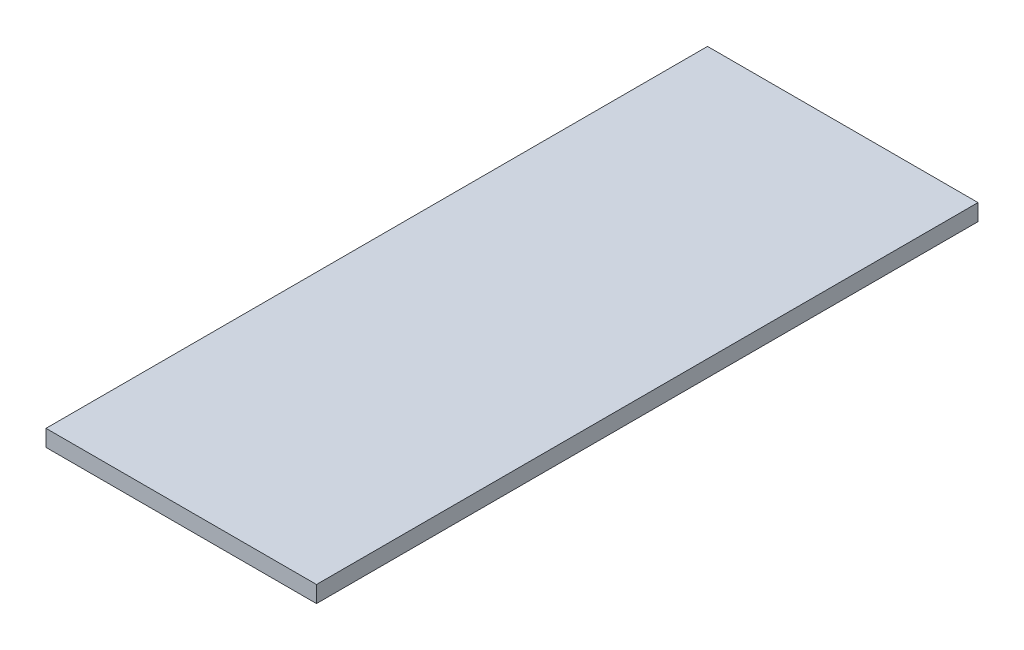
SolidWorks part; units mm, degrees
ref_plane "Спереди" through (0, 0, 0) normal (0, 0, 1) x (1, 0, 0)
ref_plane "Сверху" through (0, 0, 0) normal (0, 1, 0) x (1, 0, 0)
ref_plane "Справа" through (0, 0, 0) normal (1, 0, 0) x (0, 0, -1)
sketch "Эскиз1" plane through (0, 0, 0) normal (0, 1, 0) x (1, 0, 0)
  line L1 (147, -359.5) -> (-147, -359.5)
  line L2 (147, -359.5) -> (147, 359.5)
  line L3 (147, 359.5) -> (-147, 359.5)
  line L4 (-147, -359.5) -> (-147, 359.5)
  line L5 (147, -359.5) -> (-147, 359.5) construction
  line L6 (147, 359.5) -> (-147, -359.5) construction
  point P0 (0, 0)
  dimension "D1" = 294
  dimension "D2" = 719
extrude "Бобышка-Вытянуть1" add sketch "Эскиз1" along normal blind 18
